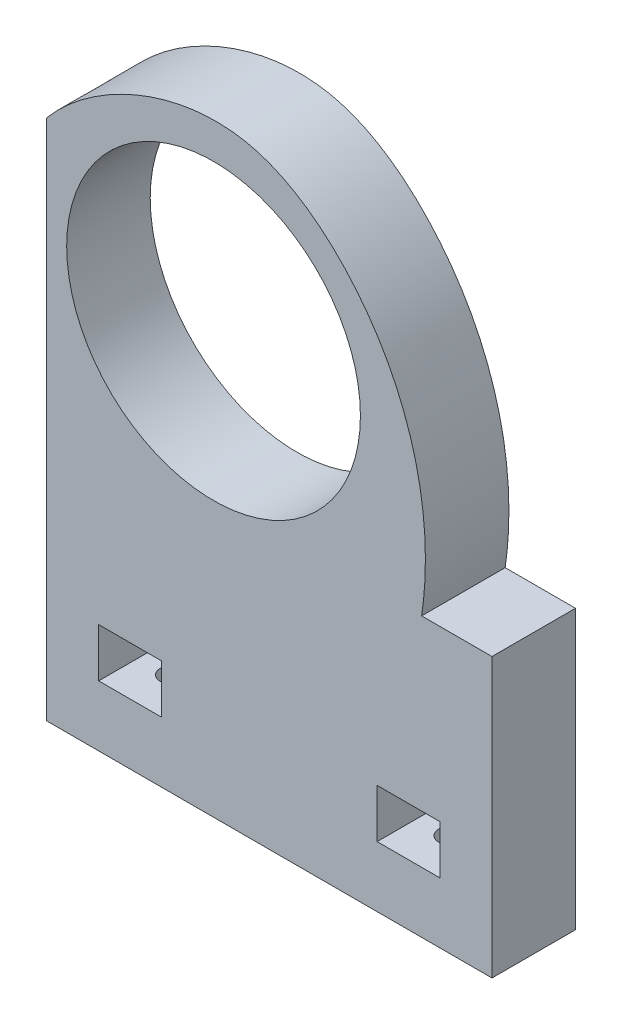
SolidWorks part; units mm, degrees
ref_plane "Front Plane" through (0, 0, 0) normal (0, 0, 1) x (1, 0, 0)
ref_plane "Top Plane" through (0, 0, 0) normal (0, 1, 0) x (1, 0, 0)
ref_plane "Right Plane" through (0, 0, 0) normal (1, 0, 0) x (0, 0, -1)
sketch "Sketch1" plane through (0, 0, 0) normal (0, 0, 1) x (1, 0, 0)
  line L0 (-32, 20) -> (-32, 55)
  line L1 (-32, -20) -> (32, -20)
  line L2 (-32, -20) -> (-32, 20)
  line L3 (-32, 20) -> (32, 20)
  line L4 (32, -20) -> (32, 20)
  line L5 (0, 20) -> (0, -20) construction
  line L6 (-32, 0) -> (32, 0) construction
  line L7 (21.8947, 20) -> (-32, 20)
  spline S0 degree 3 poles (-32, 55) (-25.4673, 62.8756) (-5.8174, 72.0293) (19.3344, 52.0752) (23.7759, 32.7099) (21.8947, 20) knots 0 0 0 0 0.370538 0.573067 1 1 1 1
  point P0 (0, 0)
  dimension "D1" = 64
  dimension "D2" = 40
  dimension "D3" = 35
extrude "Boss-Extrude1" add sketch "Sketch1" along normal blind 12 contours S0 L0 L3 | L1 L4 L3 L2
sketch "Sketch2" plane through (0, 0, 12) normal (0, 0, 1) x (1, 0, 0)
  line L0 (32, -20) -> (32, 20) construction
  line L1 (4.2, 52.5) -> (-20.2, 52.5)
  line L2 (4.2, 52.5) -> (4.2, 7.5)
  line L3 (4.2, 7.5) -> (-20.2, 7.5)
  line L4 (-20.2, 52.5) -> (-20.2, 7.5)
  line L5 (-8, 7.5) -> (-8, 52.5) construction
  line L6 (4.2, 30) -> (-20.2, 30) construction
  line L7 (-32, -20) -> (32, -20) construction
  circle A0 centre (-8, 40.5) radius 21.1
  point P0 (-8, 30)
  dimension "D6" = 42.2
  dimension "D1" = 40
  dimension "D2" = 45
  dimension "D3" = 50
  dimension "D4" = 24.4
  dimension "D5" = 12
extrude "Cut-Extrude1" cut sketch "Sketch2" against normal through all contours L2 A0 L4 L1 | L4 A0 L2 L1
sketch "Sketch3" plane through (0, -20, 0) normal (0, -1, 0) x (1, 0, 0)
  line L0 (-32, 0) -> (32, 0) construction
  circle A0 centre (-20, 6) radius 1.65
  circle A1 centre (20, 6) radius 1.65
  point P4 (0, 0)
  dimension "D3" = 3.3
  dimension "D1" = 20
  dimension "D2" = 2
extrude "Cut-Extrude4" cut sketch "Sketch3" against normal blind 10
sketch "Sketch5" plane through (0, 0, 12) normal (0, 0, 1) x (1, 0, 0)
  line L0 (-32, -20) -> (32, -20) construction
  line L1 (-24.5, -4.2829) -> (-15.5, -4.2829)
  line L2 (-24.5, -4.2829) -> (-24.5, -11.2829)
  line L3 (-24.5, -11.2829) -> (-15.5, -11.2829)
  line L4 (-15.5, -4.2829) -> (-15.5, -11.2829)
  line L5 (-20, -11.2829) -> (-20, -4.2829) construction
  line L6 (-24.5, -7.7829) -> (-15.5, -7.7829) construction
  line L7 (15.5, -4.2829) -> (15.5, -11.2829)
  line L8 (15.5, -4.2829) -> (24.5, -4.2829)
  line L9 (24.5, -4.2829) -> (24.5, -11.2829)
  line L10 (15.5, -11.2829) -> (24.5, -11.2829)
  point P0 (-20, -7.7829)
  point P7 (0, -20)
  dimension "D1" = 9
  dimension "D2" = 7
  dimension "D3" = 20
  dimension "D4" = 2
extrude "Cut-Extrude5" cut sketch "Sketch5" against normal through all
